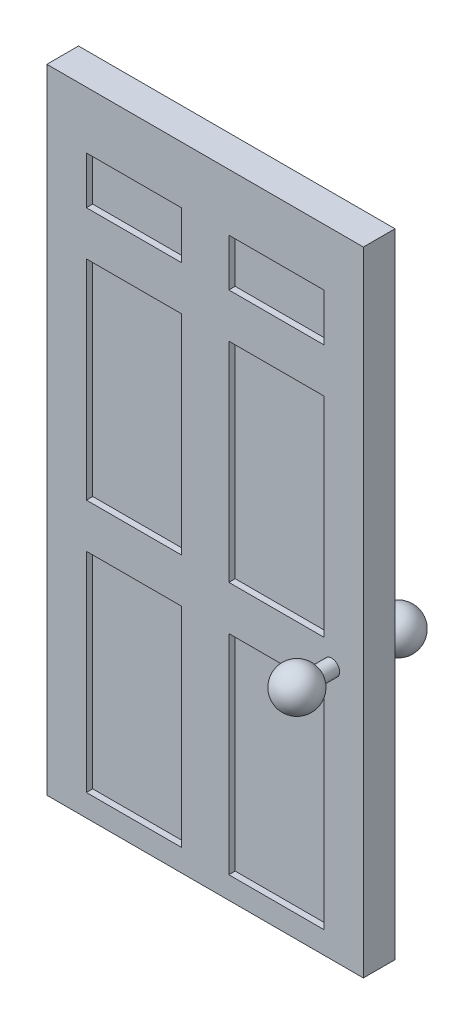
SolidWorks part; units mm, degrees
ref_plane "Front Plane" through (0, 0, 0) normal (0, 0, 1) x (1, 0, 0)
ref_plane "Top Plane" through (0, 0, 0) normal (0, 1, 0) x (1, 0, 0)
ref_plane "Right Plane" through (0, 0, 0) normal (1, 0, 0) x (0, 0, -1)
sketch "Sketch1" plane through (0, 0, 0) normal (0, 0, 1) x (1, 0, 0)
  line L1 (-25, 50) -> (25, 50)
  line L2 (-25, 50) -> (-25, -50)
  line L3 (-25, -50) -> (25, -50)
  line L4 (25, 50) -> (25, -50)
  line L5 (-25, 50) -> (25, -50) construction
  line L6 (-25, -50) -> (25, 50) construction
  point P0 (0, 0)
  dimension "D1" = 50
  dimension "D2" = 100
extrude "Boss-Extrude1" add sketch "Sketch1" along normal mid plane 5
sketch "Sketch2" plane through (0, 0, 2.5) normal (0, 0, 1) x (1, 0, 0)
  line L0 (-25, -50) -> (25, -50) construction
  line L1 (25, -50) -> (25, 50) construction
  circle A0 centre (20, -10) radius 1.25
  dimension "D3" = 2.5
  dimension "D1" = 40
  dimension "D2" = 5
extrude "Boss-Extrude2" add sketch "Sketch2" along normal blind 2.5
ref_plane "Plane1" through (20, 0, 0) normal (1, 0, 0) x (0, 0, -1)
sketch "Sketch3" plane through (20, 0, 0) normal (1, 0, 0) x (0, 0, -1)
  line L0 (-5, -8.75) -> (-5, -11.25) construction
  line L1 (-8, -6.75) -> (-8, -13.25)
  arc A0 (-8, -6.75) -> (-8, -13.25) centre (-8, -10) ccw
  dimension "D1" = 3.25
  dimension "D2" = 3
  dimension "D3" = 40
revolve "Revolve1" add sketch "Sketch3" angle 360 about L1
sketch "Sketch4" plane through (0, 0, 2.5) normal (0, 0, 1) x (1, 0, 0)
  line L0 (3.75, 0) -> (-3.75, 0) construction
  line L1 (-3.75, 41) -> (-18.75, 41)
  line L2 (-3.75, 41) -> (-3.75, 33.5)
  line L3 (-3.75, 33.5) -> (-18.75, 33.5)
  line L4 (-18.75, 41) -> (-18.75, 33.5)
  line L5 (3.75, 41) -> (18.75, 41)
  line L6 (3.75, 41) -> (3.75, 33.5)
  line L7 (3.75, 33.5) -> (18.75, 33.5)
  line L8 (18.75, 41) -> (18.75, 33.5)
  line L9 (3.75, 26.5) -> (18.75, 26.5)
  line L10 (3.75, 26.5) -> (3.75, -6.5)
  line L11 (3.75, -6.5) -> (18.75, -6.5)
  line L12 (18.75, 26.5) -> (18.75, -6.5)
  line L13 (-3.75, 26.5) -> (-18.75, 26.5)
  line L14 (-3.75, 26.5) -> (-3.75, -6.5)
  line L15 (-3.75, -6.5) -> (-18.75, -6.5)
  line L16 (-18.75, 26.5) -> (-18.75, -6.5)
  line L17 (-3.75, -13.5) -> (-18.75, -13.5)
  line L18 (-3.75, -13.5) -> (-3.75, -46.5)
  line L19 (-3.75, -46.5) -> (-18.75, -46.5)
  line L20 (-18.75, -13.5) -> (-18.75, -46.5)
  line L21 (3.75, -13.5) -> (18.75, -13.5)
  line L22 (3.75, -13.5) -> (3.75, -46.5)
  line L23 (3.75, -46.5) -> (18.75, -46.5)
  line L24 (18.75, -13.5) -> (18.75, -46.5)
  line L25 (-25, -50) -> (25, -50) construction
  point P28 (0, 0)
  dimension "D1" = 7.5
  dimension "D2" = 15
  dimension "D3" = 7
  dimension "D4" = 33
  dimension "D5" = 7
  dimension "D6" = 7.5
  dimension "D7" = 3.5
extrude "Cut-Extrude1" cut sketch "Sketch4" against normal blind 1
mirror "Mirror1" about plane through (0, 0, 0) normal (0, 0, 1) of "Boss-Extrude2", "Revolve1", "Cut-Extrude1"
